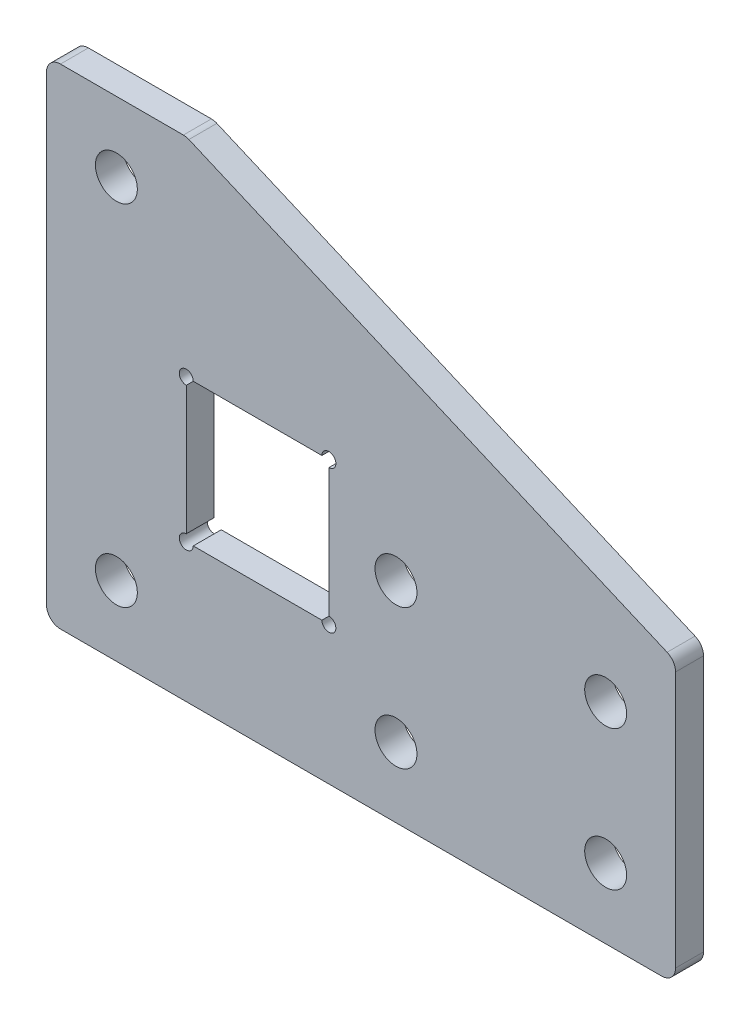
SolidWorks part; units mm, degrees
material "环氧板3240"
ref_plane "前视基准面" through (0, 0, 0) normal (0, 0, 1) x (1, 0, 0)
ref_plane "上视基准面" through (0, 0, 0) normal (0, 1, 0) x (1, 0, 0)
ref_plane "右视基准面" through (0, 0, 0) normal (1, 0, 0) x (0, 0, -1)
other "Configuration Table"
sketch "草图1" plane through (0, 0, 0) normal (0, 0, 1) x (1, 0, 0)
  line L0 (-5, 30) -> (5, 30)
  line L2 (40, 15) -> (40, -5)
  line L5 (-5, -5) -> (-5, 30)
  line L6 (0, 30) -> (0, -5) construction
  line L7 (0, 0) -> (40, 0) construction
  line L11 (40, 10) -> (0, 10) construction
  line L12 (35, 0) -> (35, 10) construction
  line L13 (20, 0) -> (20, 10) construction
  line L16 (40, 15) -> (5, 15) construction
  line L19 (15.2, 15.1) -> (15.2, 4.9)
  line L20 (40, 15) -> (5, 30)
  line L21 (5, 30) -> (5, -5) construction
  line L26 (40, 5) -> (-5, 5) construction
  line L27 (5, 4.9) -> (5, 15.1)
  line L28 (5, 15.1) -> (15.2, 15.1)
  line L29 (15.2, 4.9) -> (5, 4.9)
  line L30 (40, -5) -> (-5, -5)
  circle A1 centre (35, 0) radius 1.5
  circle A2 centre (0, 0) radius 1.5
  circle A3 centre (20, 0) radius 1.5
  circle A4 centre (0, 25) radius 1.5
  circle A5 centre (35, 10) radius 1.5
  circle A6 centre (20, 10) radius 1.5
  circle A8 centre (0, 10) radius 1.5 construction
  point P10 (15.2, 10)
  dimension "D8" = 3
  dimension "D9" = 5
  dimension "D2" = 15
  dimension "D11" = 5
  dimension "D12" = 10.2
  dimension "D15" = 15
  dimension "D6" = 35
  dimension "D1" = 20
  dimension "D3" = 10
  dimension "D4" = 45
  dimension "D5" = 10.2
  dimension "D13" = 15
  dimension "D14" = 10
extrude "凸台-拉伸1" add sketch "草图1" along normal blind 2 contours L2 L5 L0
sketch "草图2" plane through (0, 0, 2) normal (0, 0, 1) x (1, 0, 0)
  circle A0 centre (15.2, 15.1) radius 0.5
  circle A1 centre (15.2, 4.9) radius 0.5
  circle A2 centre (5, 15.1) radius 0.5
  circle A3 centre (5, 4.9) radius 0.5
  dimension "D1" = 1
extrude "切除-拉伸1" cut sketch "草图2" against normal blind 10
fillet "圆角1" radius 1 5 edges at (40, 15, 1) (5, 30, 1) (-5, 30, 1) (40, -5, 1) (-5, -5, 1)
